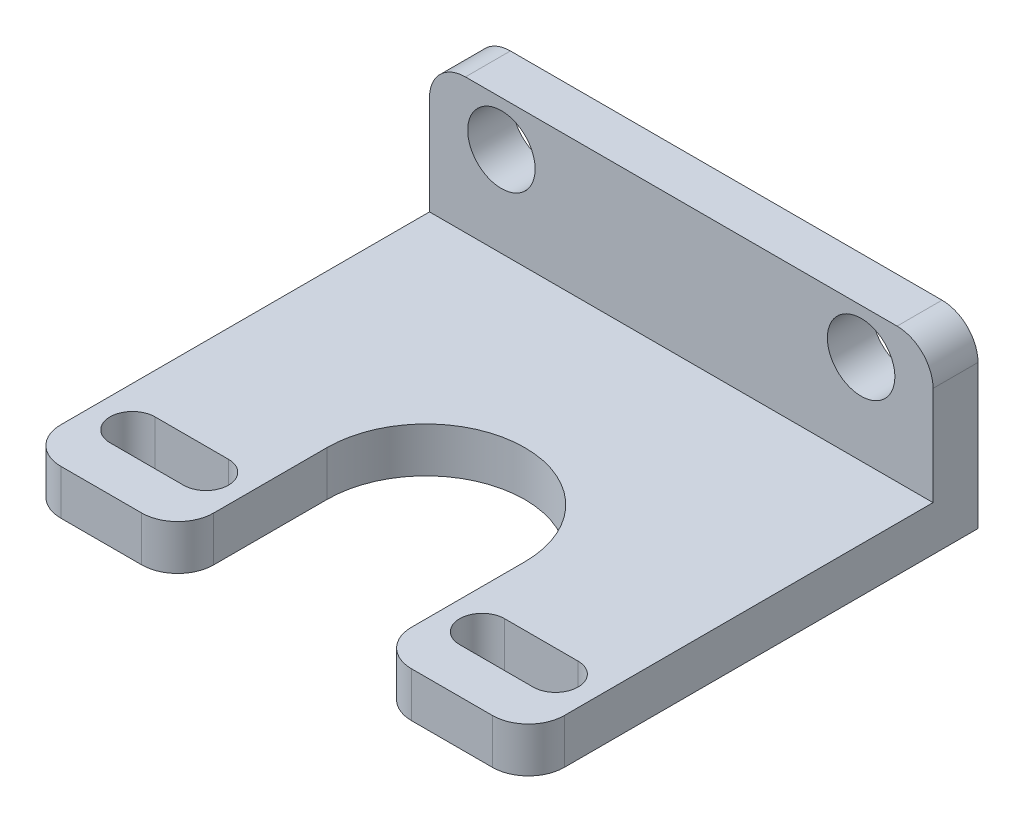
SolidWorks part; units mm, degrees
ref_plane "Front Plane" through (0, 0, 0) normal (0, 0, 1) x (1, 0, 0)
ref_plane "Top Plane" through (0, 0, 0) normal (0, 1, 0) x (1, 0, 0)
ref_plane "Right Plane" through (0, 0, 0) normal (1, 0, 0) x (0, 0, -1)
sketch "Sketch1" plane through (0, 0, 0) normal (0, 0, 1) x (1, 0, 0)
  line L0 (0, 6.35) -> (0, -6.35) construction
  line L1 (-17.78, 6.35) -> (17.78, 6.35)
  line L2 (-17.78, 6.35) -> (-17.78, -6.35)
  line L3 (-17.78, -6.35) -> (17.78, -6.35)
  line L4 (17.78, 6.35) -> (17.78, -6.35)
  circle A0 centre (-12.7, 3.175) radius 2.3813
  circle A1 centre (12.7, 3.175) radius 2.3813
  point P0 (0, 0)
  dimension "D4" = 25.4
  dimension "D1" = 17.78
  dimension "D2" = 12.7
  dimension "D3" = 17.78
extrude "Boss-Extrude1" add sketch "Sketch1" along normal blind 3.175
sketch "Sketch7" plane through (0, 0, 3.175) normal (0, 0, 1) x (1, 0, 0)
  line L1 (-17.78, -3.175) -> (17.78, -3.175)
  line L2 (-17.78, -3.175) -> (-17.78, -6.35)
  line L3 (-17.78, -6.35) -> (17.78, -6.35)
  line L4 (17.78, -3.175) -> (17.78, -6.35)
  line L5 (-17.78, -3.175) -> (17.78, -6.35) construction
  line L6 (-17.78, -6.35) -> (17.78, -3.175) construction
  point P0 (0, -4.7625)
  dimension "D1" = 3.175
extrude "Boss-Extrude3" add sketch "Sketch7" along normal blind 28.575
sketch "Sketch11" plane through (0, -6.35, 0) normal (0, -1, 0) x (1, 0, 0)
  line L3 (-6.985, 42.2919) -> (6.985, 42.2919)
  line L4 (-6.985, 42.2919) -> (-6.985, 21.2081)
  line L6 (6.985, 42.2919) -> (6.985, 21.2081)
  line L11 (-14.9388, 26.9875) -> (-9.7507, 26.9875) construction
  line L12 (-14.9388, 28.575) -> (-9.7507, 28.575)
  line L13 (-14.9388, 25.4) -> (-9.7507, 25.4)
  line L14 (14.9388, 26.9875) -> (9.7507, 26.9875) construction
  line L15 (14.9388, 28.575) -> (9.7507, 28.575)
  line L16 (14.9388, 25.4) -> (9.7507, 25.4)
  arc A0 (-14.9388, 28.575) -> (-14.9388, 25.4) centre (-14.9388, 26.9875) ccw
  arc A1 (-9.7507, 25.4) -> (-9.7507, 28.575) centre (-9.7507, 26.9875) ccw
  arc A2 (-6.985, 21.2081) -> (6.985, 21.2081) centre (0, 21.2081) ccw
  arc A3 (14.9388, 28.575) -> (14.9388, 25.4) centre (14.9388, 26.9875) cw
  arc A4 (9.7507, 25.4) -> (9.7507, 28.575) centre (9.7507, 26.9875) cw
  point P17 (-12.3447, 26.9875)
  point P26 (12.3447, 26.9875)
  dimension "D1" = 13.97
extrude "Cut-Extrude6" cut sketch "Sketch11" against normal blind 28.575
fillet "Fillet3" radius 2.54 6 edges at (6.985, -4.7625, 31.75) (17.78, -4.7625, 31.75) (-6.985, -4.7625, 31.75) (-17.78, -4.7625, 31.75) (-17.78, 6.35, 1.5875) (17.78, 6.35, 1.5875)
